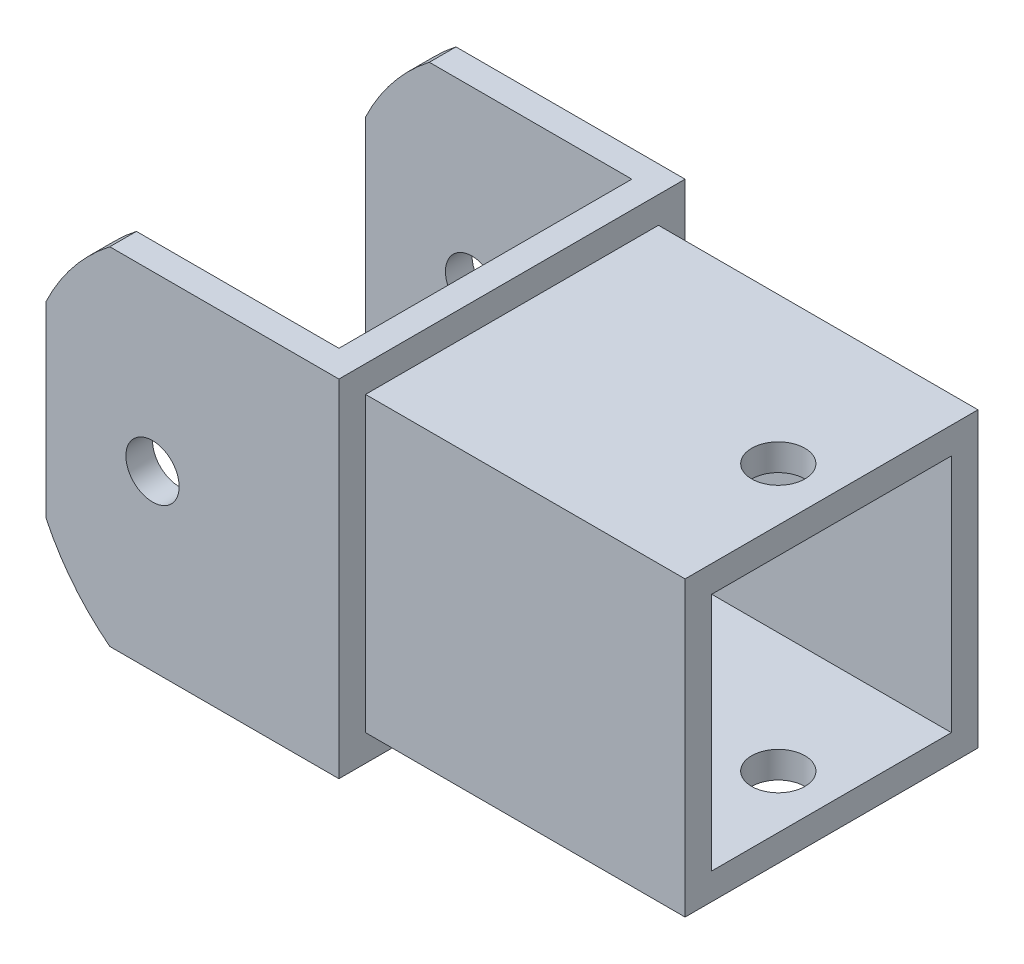
SolidWorks part; units mm, degrees
ref_plane "Front Plane" through (0, 0, 0) normal (0, 0, 1) x (1, 0, 0)
ref_plane "Top Plane" through (0, 0, 0) normal (0, 1, 0) x (1, 0, 0)
ref_plane "Right Plane" through (0, 0, 0) normal (1, 0, 0) x (0, 0, -1)
sketch "Sketch2" plane through (0, 0, 0) normal (0, 1, 0) x (1, 0, 0)
  line L0 (-50.8, 38.1) -> (76.2, 38.1)
  line L1 (76.2, 38.1) -> (76.2, -101.6)
  line L2 (76.2, -101.6) -> (-50.8, -101.6)
  line L3 (-50.8, -101.6) -> (-50.8, -114.3)
  line L4 (-50.8, -114.3) -> (88.9, -114.3)
  line L5 (88.9, -114.3) -> (88.9, 50.8)
  line L6 (88.9, 50.8) -> (-50.8, 50.8)
  line L7 (-50.8, 50.8) -> (-50.8, 38.1)
  point P2 (19.05, -114.3)
  point P9 (12.7, 38.1)
  dimension "D1" = 12.7
  dimension "D2" = 12.7
  dimension "D3" = 12.7
  dimension "D4" = 139.7
  dimension "D5" = 38.1
  dimension "D6" = 127
  dimension "D8" = 76.2
extrude "Boss-Extrude1" add sketch "Sketch2" along normal mid plane 165.1
sketch "Sketch4" plane through (88.9, 0, 0) normal (1, 0, 0) x (0, 0, -1)
  line L0 (50.8, 82.55) -> (50.8, -82.55) construction
  line L5 (-88.9, 57.15) -> (25.4, 57.15)
  line L6 (-88.9, 57.15) -> (-88.9, -57.15)
  line L11 (-88.9, -57.15) -> (25.4, -57.15)
  line L12 (25.4, 57.15) -> (25.4, -57.15)
  line L13 (-88.9, 57.15) -> (25.4, -57.15) construction
  line L14 (-88.9, -57.15) -> (25.4, 57.15) construction
  line L15 (-101.6, 69.85) -> (38.1, 69.85)
  line L16 (-101.6, 69.85) -> (-101.6, -69.85)
  line L17 (-101.6, -69.85) -> (38.1, -69.85)
  line L18 (38.1, 69.85) -> (38.1, -69.85)
  line L19 (-101.6, 69.85) -> (38.1, -69.85) construction
  line L20 (-101.6, -69.85) -> (38.1, 69.85) construction
  line L21 (-114.3, 82.55) -> (-114.3, -82.55) construction
  line L25 (-114.3, 82.55) -> (50.8, 82.55) construction
  point P0 (-31.75, 0)
  point P6 (-31.75, 0)
  dimension "D1" = 69.85
  dimension "D2" = 82.55
  dimension "D3" = 165.1
  dimension "D4" = 12.7
  dimension "D5" = 12.7
  dimension "D6" = 12.7
extrude "Boss-Extrude2" add sketch "Sketch4" along normal blind 152.4
sketch "Sketch5" plane through (0, 0, 114.3) normal (0, 0, 1) x (1, 0, 0)
  circle A0 centre (0, 0) radius 12.7
  dimension "D1" = 25.4
extrude "Cut-Extrude1" cut sketch "Sketch5" against normal through all both and the other way through all
sketch "Sketch6" plane through (0, 69.85, 0) normal (0, 1, 0) x (1, 0, 0)
  line L0 (241.3, 38.1) -> (241.3, -101.6) construction
  line L1 (241.3, 38.1) -> (88.9, 38.1) construction
  circle A0 centre (215.9, -31.75) radius 12.7
  dimension "D1" = 25.4
  dimension "D2" = 25.4
  dimension "D3" = 69.85
extrude "Cut-Extrude2" cut sketch "Sketch6" against normal through all both and the other way through all
sketch "Sketch7" plane through (0, 0, 114.3) normal (0, 0, 1) x (1, 0, 0)
  line L0 (-50.8, 82.55) -> (88.9, 82.55) construction
  line L1 (-50.8, -82.55) -> (88.9, -82.55) construction
  line L2 (-20.3743, 82.55) -> (-68.4291, 82.55)
  line L3 (-68.4291, 82.55) -> (-68.4291, -82.55)
  line L4 (-68.4291, -82.55) -> (-20.3743, -82.55)
  arc A0 (-20.3743, 82.55) -> (-20.3743, -82.55) centre (43.5565, 0) ccw
extrude "Cut-Extrude4" cut sketch "Sketch7" against normal through all both and the other way through all contours L3 L4 A0 L2
move or copy body "Body-Move/Copy1" bodies to move or copy 106 copy no rotation origin (0, 0, 31.7503) rotation axis (1, 0, 0) rotation angle 90
move or copy body "Body-Move/Copy2" bodies to move or copy 107 copy no rotation origin (0, 0, 31.7502) rotation axis (-1, 0, 0) rotation angle 90
